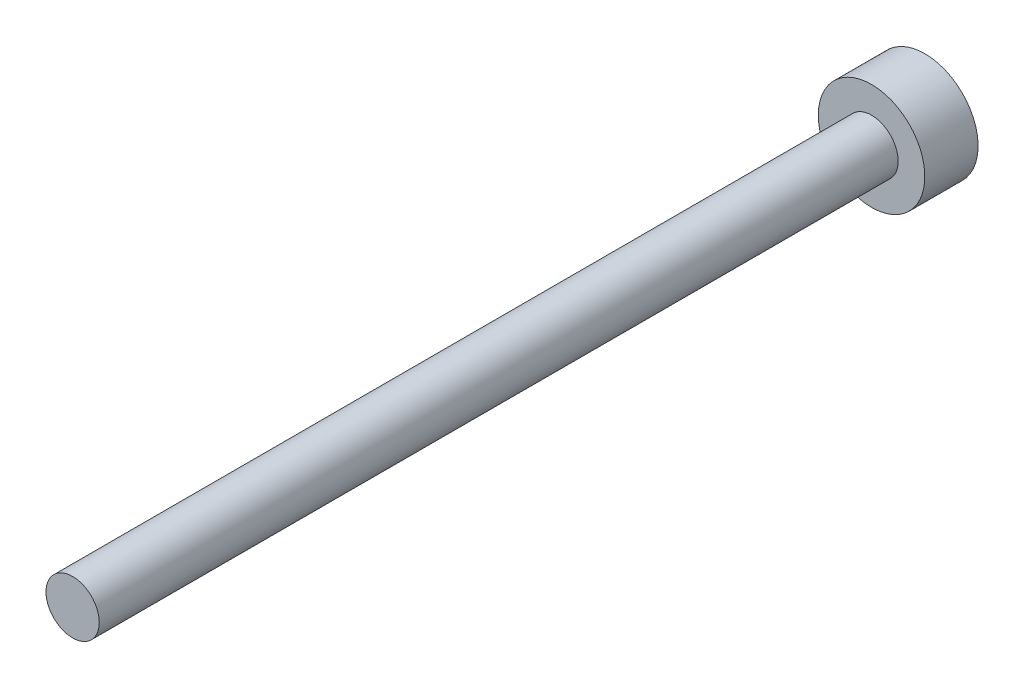
SolidWorks part; units mm, degrees
ref_plane "前视基准面" through (0, 0, 0) normal (0, 0, 1) x (1, 0, 0)
ref_plane "上视基准面" through (0, 0, 0) normal (0, 1, 0) x (1, 0, 0)
ref_plane "右视基准面" through (0, 0, 0) normal (1, 0, 0) x (0, 0, -1)
sketch "草图1" plane through (0, 0, 0) normal (0, 0, 1) x (1, 0, 0)
  circle A0 centre (0, 0) radius 1.5
  dimension "D1" = 3
extrude "凸台-拉伸1" add sketch "草图1" along normal blind 45
cosmetic thread "装饰螺纹线1" parameters "D2"=2
sketch "草图2" plane through (0, 0, 0) normal (0, 0, -1) x (-1, 0, 0)
  circle A0 centre (0, 0) radius 3
  dimension "D1" = 6
extrude "凸台-拉伸2" add sketch "草图2" along normal blind 3
